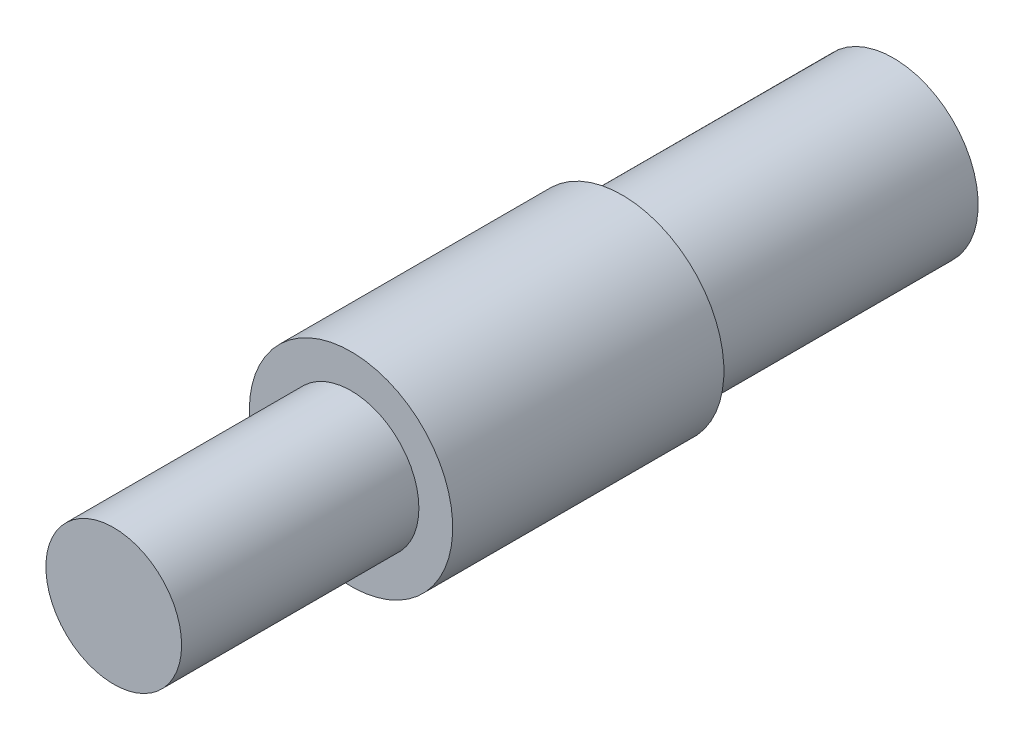
SolidWorks part; units mm, degrees
ref_plane "Front Plane" through (0, 0, 0) normal (0, 0, 1) x (1, 0, 0)
ref_plane "Top Plane" through (0, 0, 0) normal (0, 1, 0) x (1, 0, 0)
ref_plane "Right Plane" through (0, 0, 0) normal (1, 0, 0) x (0, 0, -1)
sketch "Sketch2" plane through (0, 0, 0) normal (0, 0, 1) x (1, 0, 0)
  circle A0 centre (0, 0) radius 10.01
  dimension "D1" = 20.02
extrude "Boss-Extrude1" add sketch "Sketch2" against normal blind 35
sketch "Sketch3" plane through (0, 0, -35) normal (0, 0, -1) x (-1, 0, 0)
  circle A0 centre (0, 0) radius 15
  dimension "D1" = 30
extrude "Boss-Extrude2" add sketch "Sketch3" along normal blind 40
sketch "Sketch4" plane through (0, 0, -75) normal (0, 0, -1) x (-1, 0, 0)
  circle A0 centre (0, 0) radius 12.5
  dimension "D1" = 25
extrude "Boss-Extrude3" add sketch "Sketch4" along normal blind 40
